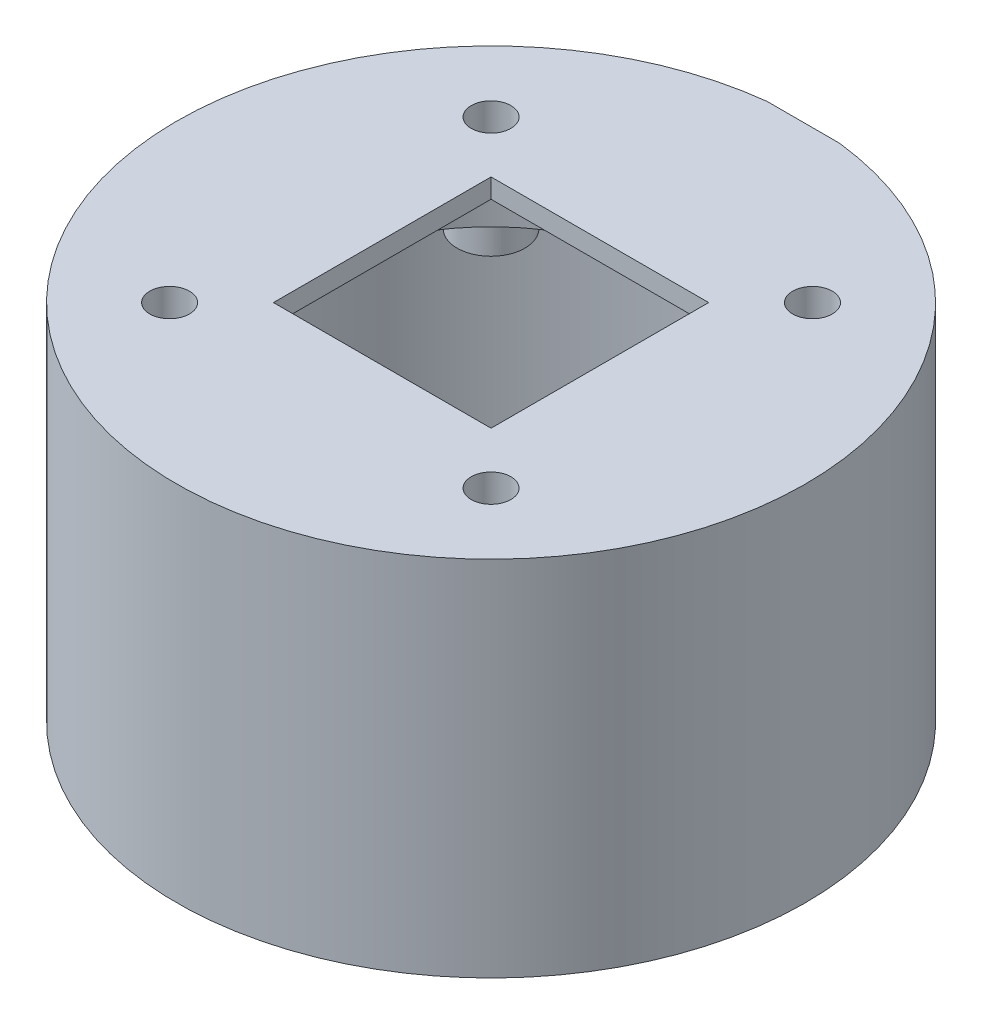
SolidWorks part; units mm, degrees
ref_plane "Спереди" through (0, 0, 0) normal (0, 0, 1) x (1, 0, 0)
ref_plane "Сверху" through (0, 0, 0) normal (0, 1, 0) x (1, 0, 0)
ref_plane "Справа" through (0, 0, 0) normal (1, 0, 0) x (0, 0, -1)
sketch "Sketch1" plane through (0, 0, 0) normal (0, 1, 0) x (1, 0, 0)
  circle A0 centre (0, 0) radius 60
  circle A1 centre (0, 0) radius 65
  dimension "D1" = 120
  dimension "D2" = 130
extrude "Boss-Extrude1" add sketch "Sketch1" along normal blind 55
sketch "Sketch2" plane through (0, 55, 0) normal (0, 1, 0) x (1, 0, 0)
  circle A0 centre (0, 0) radius 65
  circle A1 centre (0, 0) radius 65 construction
extrude "Boss-Extrude2" add sketch "Sketch2" along normal blind 20
sketch "Sketch3" plane through (0, 75, 0) normal (0, 1, 0) x (1, 0, 0)
  line L1 (33.234, 33.234) -> (-33.234, 33.234) construction
  line L2 (33.234, 33.234) -> (33.234, -33.234) construction
  line L3 (33.234, -33.234) -> (-33.234, -33.234) construction
  line L4 (-33.234, 33.234) -> (-33.234, -33.234) construction
  line L5 (33.234, 33.234) -> (-33.234, -33.234) construction
  line L6 (33.234, -33.234) -> (-33.234, 33.234) construction
  line L7 (22.5, 22.5) -> (-22.5, 22.5)
  line L8 (22.5, 22.5) -> (22.5, -22.5)
  line L9 (22.5, -22.5) -> (-22.5, -22.5)
  line L10 (-22.5, 22.5) -> (-22.5, -22.5)
  line L11 (22.5, 22.5) -> (-22.5, -22.5) construction
  line L12 (22.5, -22.5) -> (-22.5, 22.5) construction
  circle A0 centre (0, 0) radius 47 construction
  circle A1 centre (-33.234, -33.234) radius 4.1
  circle A2 centre (-33.234, 33.234) radius 4.1
  circle A3 centre (33.234, 33.234) radius 4.1
  circle A4 centre (33.234, -33.234) radius 4.1
  dimension "D1" = 94
  dimension "D2" = 8.2
  dimension "D3" = 45
extrude "Cut-Extrude1" cut sketch "Sketch3" against normal through all
sketch "Sketch5" plane through (0, 55, 0) normal (0, -1, 0) x (1, 0, 0)
  line L0 (0, 22.5) -> (0, 60) construction
  line L1 (-22.5, 22.5) -> (22.5, 22.5) construction
  line L3 (-22.5, 42.5) -> (22.5, 42.5)
  line L4 (-22.5, 42.5) -> (-22.5, 22.5)
  line L5 (-22.5, 22.5) -> (22.5, 22.5)
  line L6 (22.5, 42.5) -> (22.5, 22.5)
  line L7 (-22.5, 42.5) -> (22.5, 22.5) construction
  line L8 (-22.5, 22.5) -> (22.5, 42.5) construction
  circle A0 centre (0, 0) radius 60 construction
  point P7 (0, 32.5)
  dimension "D1" = 20
extrude "Cut-Extrude2" cut sketch "Sketch5" against normal blind 18
sketch "Sketch6" plane through (0, 55, 0) normal (0, -1, 0) x (1, 0, 0)
  circle A0 centre (0, 0) radius 51
  dimension "D1" = 102
extrude "Cut-Extrude3" cut sketch "Sketch6" against normal blind 6
sketch "Sketch7" plane through (0, 61, 0) normal (0, -1, 0) x (1, 0, 0)
  circle A0 centre (-33.234, -33.234) radius 7
  circle A1 centre (-33.234, 33.234) radius 7
  circle A2 centre (-33.234, 33.234) radius 4.1
  circle A3 centre (-33.234, -33.234) radius 4.1
  circle A4 centre (33.234, -33.234) radius 4.1
  circle A5 centre (33.234, 33.234) radius 4.1
  circle A6 centre (33.234, -33.234) radius 7
  circle A7 centre (33.234, 33.234) radius 7
  dimension "D1" = 14
extrude "Boss-Extrude3" add sketch "Sketch7" along normal up to surface (6 mm away) up to face at (0, 55, 0)
sketch "Sketch8" plane through (0, 61, 0) normal (0, -1, 0) x (1, 0, 0)
  circle A0 centre (0, 0) radius 39
  dimension "D1" = 78
extrude "Cut-Extrude4" cut sketch "Sketch8" against normal blind 10
sketch "Sketch9" plane through (0, 0, 0) normal (0, -1, 0) x (1, 0, 0)
  line L0 (0, -65) -> (0, 65) construction
  line L1 (7.5, -64.5659) -> (-7.5, -64.5659)
  circle A0 centre (0, 0) radius 65 construction
  point P8 (0, -64.5659)
  dimension "D1" = 15
extrude "Cut-Extrude5" cut sketch "Sketch9" against normal through all and the other way through all
sketch "Sketch10" plane through (0, 0, -64.5659) normal (0, 0, -1) x (-1, 0, 0)
  line L0 (0, 0) -> (0, 75) construction
  line L1 (-7.5, 0) -> (7.5, 0) construction
  line L2 (-7.5, 75) -> (7.5, 75) construction
  line L4 (-7.5, 20.4) -> (7.5, 20.4)
  line L5 (-7.5, 20.4) -> (-7.5, 7.6)
  line L6 (-7.5, 7.6) -> (7.5, 7.6)
  line L7 (7.5, 20.4) -> (7.5, 7.6)
  line L8 (-7.5, 20.4) -> (7.5, 7.6) construction
  line L9 (-7.5, 7.6) -> (7.5, 20.4) construction
  point P6 (0, 14)
  dimension "D1" = 12.8
  dimension "D2" = 15
  dimension "D3" = 14
extrude "Cut-Extrude6" cut sketch "Sketch10" against normal blind 10
sketch "Sketch11" plane through (0, 0, -64.5659) normal (0, 0, -1) x (-1, 0, 0)
  line L0 (0, 20.4) -> (0, 7.6) construction
  line L1 (7.5, 20.4) -> (-7.5, 20.4) construction
  line L2 (-7.5, 7.6) -> (7.5, 7.6) construction
  line L4 (-10, 4) -> (10, 4)
  line L5 (-10, 4) -> (-10, 24)
  line L6 (-10, 24) -> (10, 24)
  line L7 (10, 4) -> (10, 24)
  line L8 (-10, 4) -> (10, 24) construction
  line L9 (-10, 24) -> (10, 4) construction
  point P6 (0, 14)
  dimension "D1" = 20
  dimension "D2" = 20
extrude "Cut-Extrude7" cut sketch "Sketch11" against normal blind 10 from offset 3 offset against normal yes
sketch "Sketch12" plane through (0, 55, 0) normal (0, -1, 0) x (1, 0, 0)
  line L0 (0, 51) -> (0, 60) construction
  arc A0 (31.5902, 40.0383) -> (-31.5902, 40.0383) centre (0, 0) ccw construction
  circle A1 centre (0, 0) radius 60 construction
  circle A2 centre (0, 51) radius 7.5
  dimension "D1" = 15
extrude "Cut-Extrude8" cut sketch "Sketch12" against normal up to surface (6 mm away) up to face at (0, 61, 19.4638)
sketch "Sketch13" plane through (0, 55, 0) normal (0, -1, 0) x (1, 0, 0)
  line L0 (-60, 0) -> (-51, 0) construction
  circle A0 centre (0, 0) radius 60 construction
  arc A1 (-40.0383, 31.5902) -> (-40.0383, -31.5902) centre (0, 0) ccw construction
  circle A2 centre (-51, 0) radius 10.5
  dimension "D1" = 21
extrude "Cut-Extrude9" cut sketch "Sketch13" against normal up to surface (6 mm away) and the other way through all up to face at (0, 61, 10.1144)
